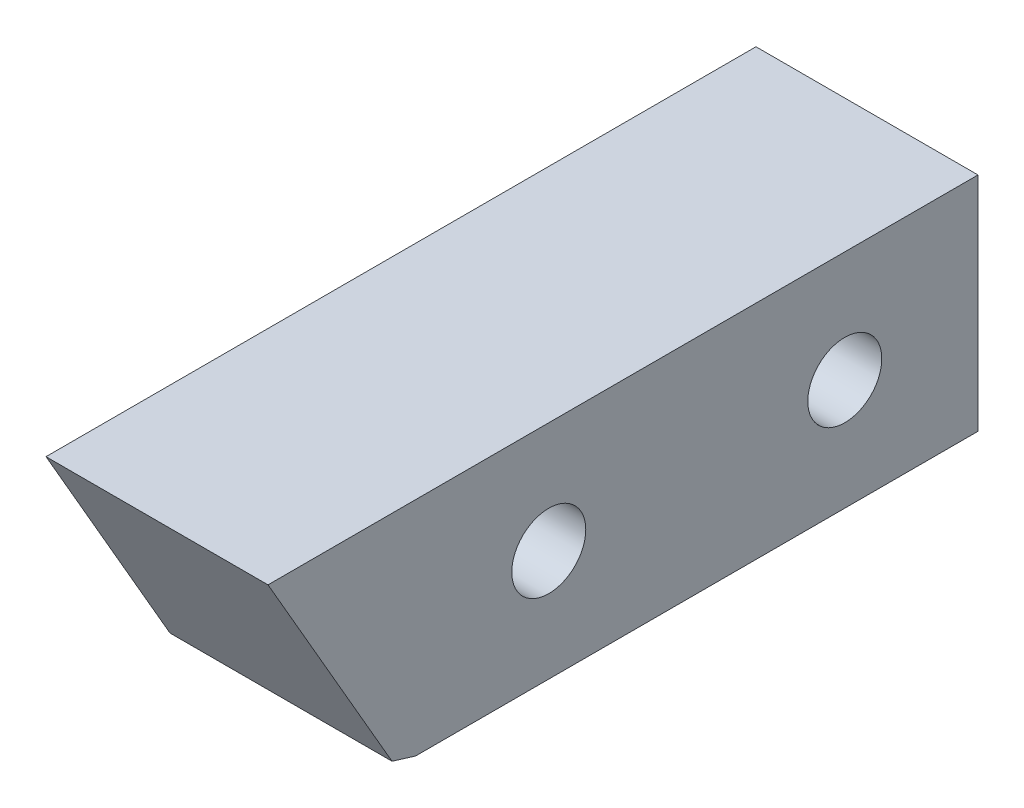
SolidWorks part; units mm, degrees
ref_plane "Front Plane" through (0, 0, 0) normal (0, 0, 1) x (1, 0, 0)
ref_plane "Top Plane" through (0, 0, 0) normal (0, 1, 0) x (1, 0, 0)
ref_plane "Right Plane" through (0, 0, 0) normal (1, 0, 0) x (0, 0, -1)
sketch "Sketch1" plane through (0, 0, 0) normal (0, 1, 0) x (1, 0, 0)
  line L1 (-4.7625, -12.065) -> (4.7625, -12.065)
  line L2 (-4.7625, -12.065) -> (-4.7625, 12.065)
  line L3 (-4.7625, 12.065) -> (4.7625, 12.065)
  line L4 (4.7625, -12.065) -> (4.7625, 12.065)
  line L5 (-4.7625, -12.065) -> (4.7625, 12.065) construction
  line L6 (-4.7625, 12.065) -> (4.7625, -12.065) construction
  point P0 (0, 0)
  dimension "D1" = 24.13
  dimension "D2" = 9.525
extrude "Extrude1" add sketch "Sketch1" along normal blind 9.525
sketch "Sketch2" plane through (4.7625, 0, 0) normal (1, 0, 0) x (0, 0, -1)
  line L0 (-12.065, 4.7625) -> (0, 4.7625) construction
  line L1 (-12.065, 9.525) -> (-12.065, 0) construction
  line L2 (0, 4.7625) -> (0, 0) construction
  circle A0 centre (-6.35, 4.7625) radius 1.5875
  circle A1 centre (6.35, 4.7625) radius 1.5875
  dimension "D1" = 3.175
  dimension "D2" = 12.7
extrude "Extrude2" cut sketch "Sketch2" against normal through all
sketch "Sketch3" plane through (4.7625, 0, 0) normal (1, 0, 0) x (0, 0, -1)
  line L0 (-12.065, 9.525) -> (-18.3943, 9.525)
  line L1 (-47.625, 9.525) -> (-18.415, 9.525) construction
  line L2 (-18.3943, 9.525) -> (-13.0744, 0.3106)
  line L3 (-13.0744, 0.3106) -> (-12.065, 0)
  line L4 (-13.8116, 0.8255) -> (-18.415, 8.7988) construction
  line L5 (-12.065, 9.525) -> (-12.065, 0)
  dimension "D1" = 0.381
extrude "Extrude3" add sketch "Sketch3" against normal through all
